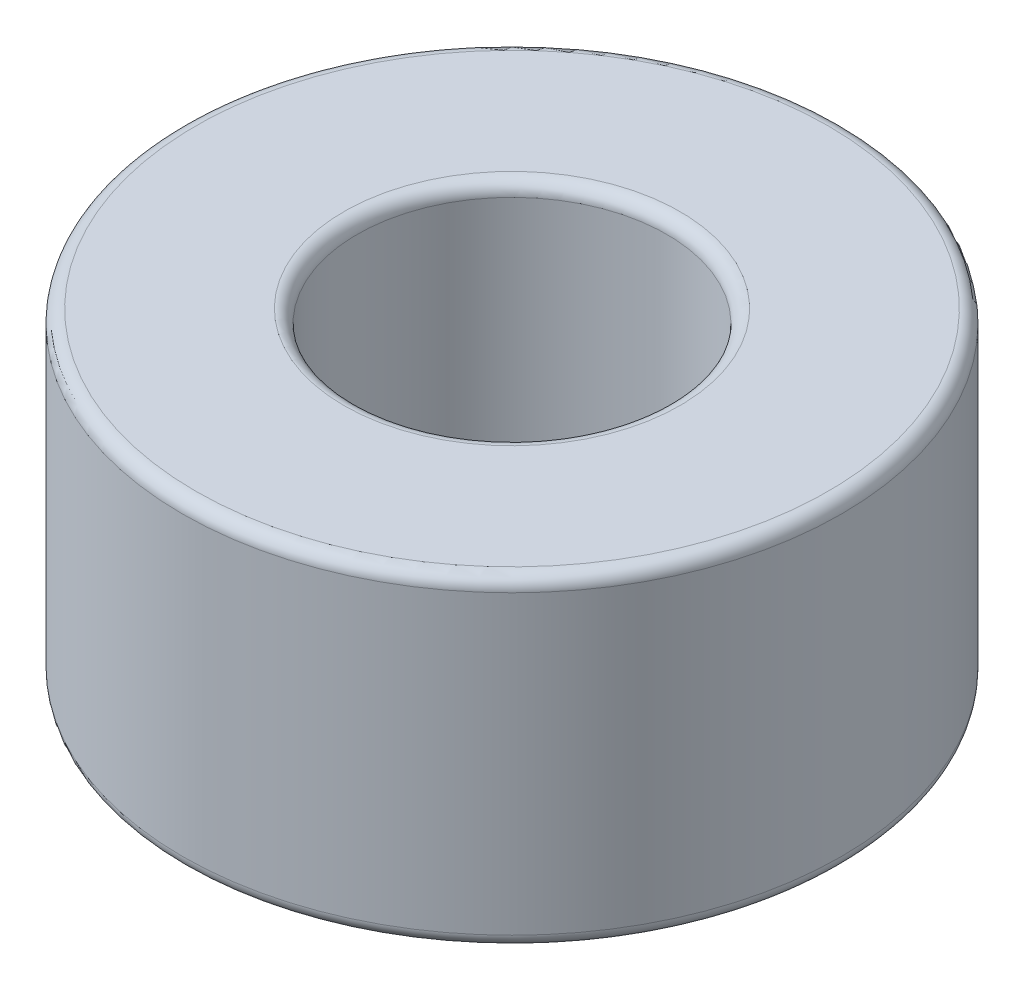
SolidWorks part; units mm, degrees
ref_plane "Front Plane" through (0, 0, 0) normal (0, 0, 1) x (1, 0, 0)
ref_plane "Top Plane" through (0, 0, 0) normal (0, 1, 0) x (1, 0, 0)
ref_plane "Right Plane" through (0, 0, 0) normal (1, 0, 0) x (0, 0, -1)
other "Bounding Box"
ref_plane "Default Plane" through (13.8565, 3.175, 6.7999) normal (0, -1, 0) x (-1, 0, 0)
sketch "Sketch1" plane through (0, 0, 0) normal (0, 1, 0) x (1, 0, 0)
  circle A0 centre (0, 0) radius 2.9845
  circle A1 centre (0, 0) radius 6.35
  dimension "D1" = 5.969
  dimension "D2" = 12.7
extrude "Boss-Extrude1" add sketch "Sketch1" along normal blind 6.223
fillet "Fillet1" radius 0.254 4 edges at (0, 0, 2.9845) (0, 0, 6.35) (0, 6.223, 6.35) (0, 6.223, 2.9845)
